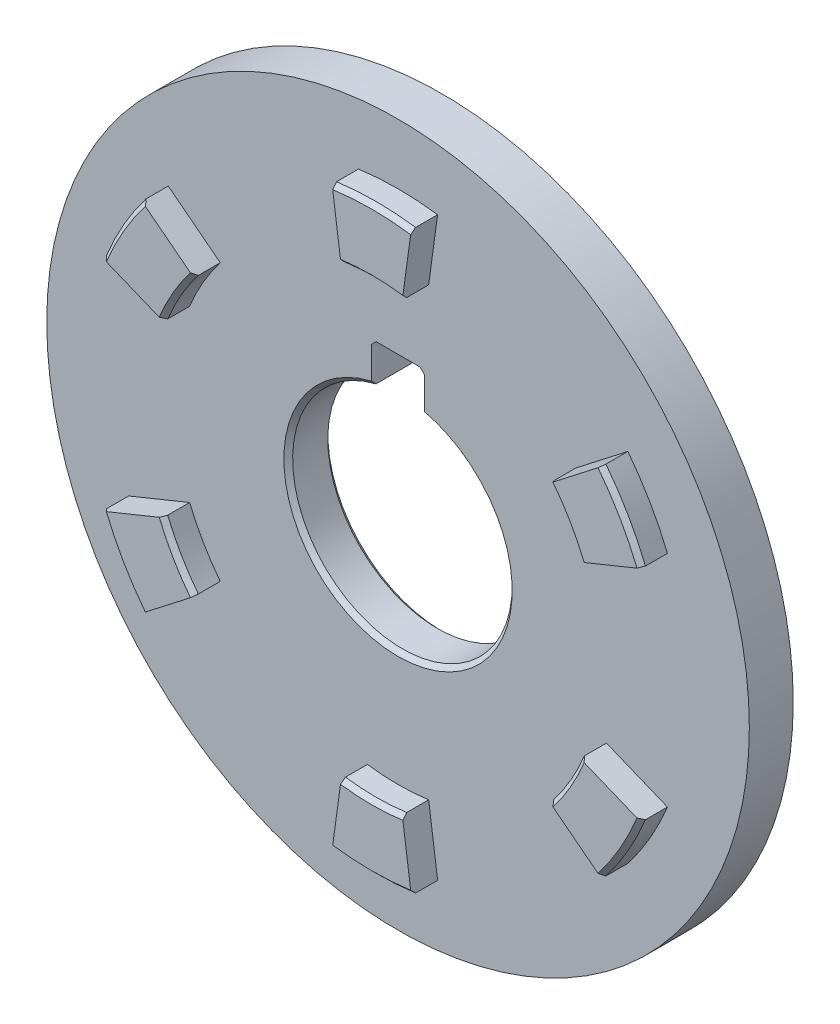
SolidWorks part; units mm, degrees
material "AISI 4340 Steel, normalized"
ref_plane "Front Plane" through (0, 0, 0) normal (0, 0, 1) x (1, 0, 0)
ref_plane "Top Plane" through (0, 0, 0) normal (0, 1, 0) x (1, 0, 0)
ref_plane "Right Plane" through (0, 0, 0) normal (1, 0, 0) x (0, 0, -1)
sketch "Sketch1" plane through (0, 0, 0) normal (0, 0, 1) x (1, 0, 0)
  line L0 (0, 0) -> (0, 33.6) construction
  line L1 (6, 24.2693) -> (6, 33.6)
  line L2 (-6, 24.2693) -> (-6, 33.6)
  line L4 (6, 33.6) -> (-6, 33.6)
  line L5 (6, 0) -> (6, 33.6) construction
  line L6 (-6, 0) -> (-6, 33.6) construction
  arc A0 (-6, 24.2693) -> (6, 24.2693) centre (0, 0) ccw
  circle A1 centre (0, 0) radius 80
  dimension "D1" = 50
  dimension "D2" = 160
  dimension "D3" = 33.6
  dimension "D4" = 6
  dimension "D5" = 6
extrude "Boss-Extrude1" add sketch "Sketch1" along normal mid plane 10
sketch "Sketch2" plane through (0, 0, 5) normal (0, 0, 1) x (1, 0, 0)
  line L0 (0, 0) -> (10.9987, 80.1156)
  line L1 (0, 0) -> (-11.9628, 87.1383)
  line L2 (0, 0) -> (0, 95.2197) construction
  line L3 (0, 0) -> (74.8815, 30.5326)
  line L4 (0, 0) -> (69.4826, 53.9293)
  line L5 (0, 0) -> (63.8828, -49.583)
  line L6 (0, 0) -> (81.4454, -33.209)
  line L7 (0, 0) -> (-10.9987, -80.1156)
  line L8 (0, 0) -> (11.9628, -87.1383)
  line L9 (0, 0) -> (-74.8815, -30.5326)
  line L10 (0, 0) -> (-69.4826, -53.9293)
  line L11 (0, 0) -> (-63.8828, 49.583)
  line L12 (0, 0) -> (-81.4454, 33.209)
  circle A0 centre (0, 0) radius 58.75 construction
  circle A1 centre (0, 0) radius 66.25
  circle A2 centre (0, 0) radius 51.25
  point P23 (0, 0)
  dimension "D1" = 117.5
  dimension "D4" = 15.634
  dimension "D2" = 7.5
  dimension "D3" = 7.5
  dimension "D5" = 6
extrude "Boss-Extrude2" add sketch "Sketch2" along normal blind 6 contours A2 L0 A1 L1 | A2 L3 A1 L4 | A2 L5 A1 L6 | A2 L7 A1 L8 | A2 L9 A1 L10 | A2 L11 A1 L12
chamfer "Chamfer1" distance 1 12 edges at (44.3838, -25.625, 11) (57.3742, -33.125, 11) (0, -66.25, 11) (0, -51.25, 11) (44.3838, 25.625, 11) (57.3742, 33.125, 11) (-57.3742, -33.125, 11) (-44.3838, -25.625, 11) (-57.3742, 33.125, 11) (-44.3838, 25.625, 11) (0, 51.25, 11) (0, 66.25, 11)
mirror "Mirror1" about plane through (0, 0, 0) normal (0, 0, 1) of "Boss-Extrude2", "Chamfer1"
chamfer "Chamfer2" distance 1 2 edges at (0, -25, -5) (0, -25, 5)
chamfer "Chamfer3" distance 1 2 edges at (6, 33.6, 0) (-6, 33.6, 0)
